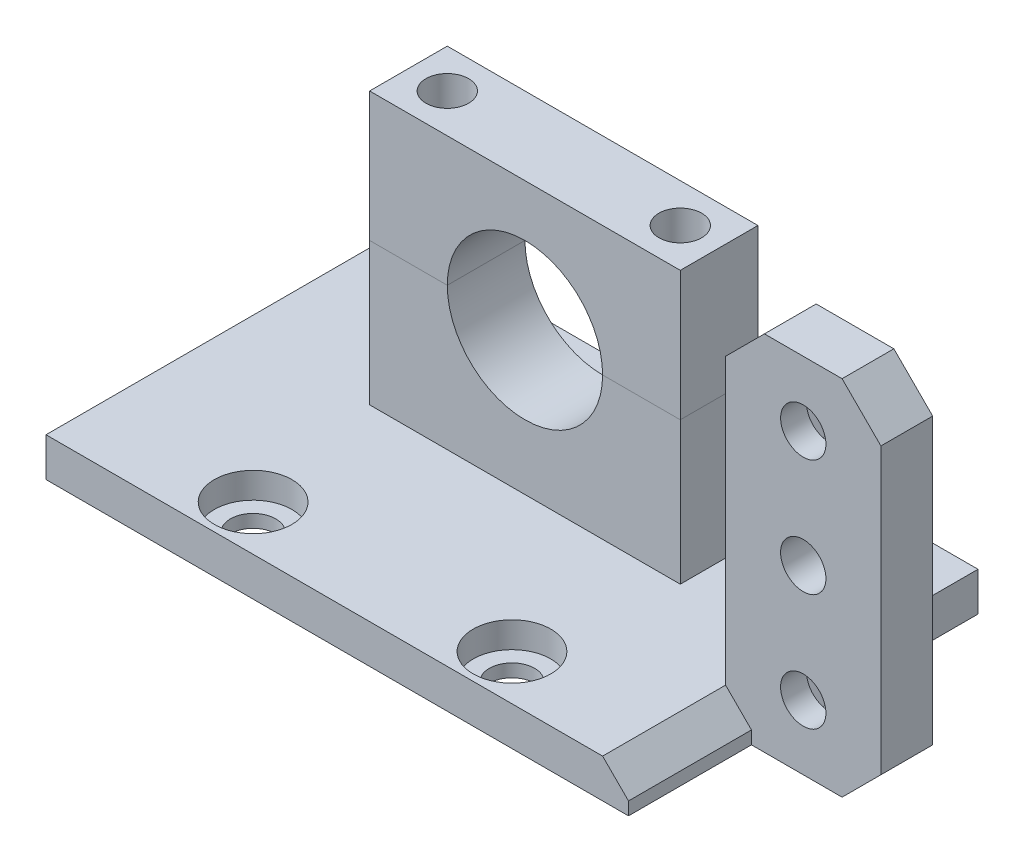
SolidWorks part; units mm, degrees
ref_plane "Front Plane" through (0, 0, 0) normal (0, 0, 1) x (1, 0, 0)
ref_plane "Top Plane" through (0, 0, 0) normal (0, 1, 0) x (1, 0, 0)
ref_plane "Right Plane" through (0, 0, 0) normal (1, 0, 0) x (0, 0, -1)
sketch "Sketch1" plane through (0, 0, 0) normal (0, 1, 0) x (1, 0, 0)
  line L1 (-22.5, -13.5) -> (22.5, -13.5)
  line L2 (-22.5, -13.5) -> (-22.5, 13.5)
  line L3 (-22.5, 13.5) -> (22.5, 13.5)
  line L4 (22.5, -13.5) -> (22.5, 13.5)
  line L5 (-22.5, -13.5) -> (22.5, 13.5) construction
  line L6 (-22.5, 13.5) -> (22.5, -13.5) construction
  point P0 (0, 0)
  dimension "D1" = 27
  dimension "D2" = 45
extrude "Boss-Extrude1" add sketch "Sketch1" along normal blind 3
sketch "Sketch2" plane through (0, 3, 0) normal (0, 1, 0) x (1, 0, 0)
  line L0 (0, 13.5) -> (0, -13.5) construction
  line L1 (22.5, 13.5) -> (-22.5, 13.5) construction
  line L2 (-22.5, -13.5) -> (22.5, -13.5) construction
  line L3 (-22.5, 0) -> (22.5, 0) construction
  line L4 (-22.5, 13.5) -> (-22.5, -13.5) construction
  line L5 (22.5, -13.5) -> (22.5, 13.5) construction
  circle A0 centre (-10, 10) radius 1.75
  circle A1 centre (10, 10) radius 1.75
  circle A2 centre (10, -10) radius 1.75
  circle A3 centre (-10, -10) radius 1.75
  dimension "D1" = 3.5
  dimension "D2" = 10
  dimension "D3" = 10
extrude "Cut-Extrude1" cut sketch "Sketch2" against normal up to next
sketch "Sketch3" plane through (0, 3, 0) normal (0, 1, 0) x (1, 0, 0)
  line L0 (0, 13.5) -> (0, -13.5) construction
  line L1 (22.5, 13.5) -> (-22.5, 13.5) construction
  line L2 (-22.5, -13.5) -> (22.5, -13.5) construction
  line L3 (-22.5, 0) -> (22.5, 0) construction
  line L4 (-22.5, 13.5) -> (-22.5, -13.5) construction
  line L5 (22.5, -13.5) -> (22.5, 13.5) construction
  circle A0 centre (-10, 10) radius 3
  circle A1 centre (10, 10) radius 3
  circle A2 centre (10, -10) radius 3
  circle A3 centre (-10, -10) radius 3
  dimension "D1" = 6
extrude "Cut-Extrude2" cut sketch "Sketch3" against normal blind 2
ref_plane "Plane1" through (0, 0, -4) normal (0, 0, 1) x (1, 0, 0)
sketch "Sketch5" plane through (0, 0, -4) normal (0, 0, 1) x (1, 0, 0)
  line L0 (0, 0) -> (0, 14) construction
  line L1 (22.5, 3) -> (-22.5, 3) construction
  line L2 (12, 3) -> (-12, 3)
  line L3 (-12, 3) -> (-12, 14)
  line L4 (-12, 14) -> (-6, 14)
  line L5 (12, 14) -> (6, 14)
  line L6 (12, 3) -> (12, 14)
  arc A0 (-6, 14) -> (6, 14) centre (0, 14) ccw
  point P13 (0, 3)
  dimension "D3" = 12
  dimension "D1" = 11
  dimension "D2" = 6
extrude "Boss-Extrude2" add sketch "Sketch5" along normal mid plane 6
sketch "Sketch6" plane through (0, 0, -4) normal (0, 0, 1) x (1, 0, 0)
  line L6 (6, 14) -> (12, 14)
  line L7 (-12, 14) -> (-6, 14)
  line L8 (-12, 14) -> (-12, 24)
  line L9 (-12, 24) -> (12, 24)
  line L10 (12, 14) -> (12, 24)
  arc A1 (6, 14) -> (-6, 14) centre (0, 14) ccw
  dimension "D1" = 24
  dimension "D2" = 10
extrude "Boss-Extrude3" add sketch "Sketch6" along normal mid plane 6 separate body
sketch "Sketch7" plane through (0, 24, 0) normal (0, 1, 0) x (1, 0, 0)
  line L0 (-12, 4) -> (12, 4) construction
  line L1 (-12, 1) -> (-12, 7) construction
  line L2 (12, 1) -> (12, 7) construction
  line L3 (0, 7) -> (0, 1) construction
  line L4 (12, 7) -> (-12, 7) construction
  line L5 (-12, 1) -> (12, 1) construction
  circle A0 centre (-9, 4) radius 1.65
  circle A1 centre (9, 4) radius 1.65
  dimension "D1" = 3.3
  dimension "D2" = 3
extrude "Cut-Extrude3" cut sketch "Sketch7" against normal blind 15
sketch "Sketch8" plane through (0, 3, 0) normal (0, 1, 0) x (1, 0, 0)
  line L0 (-22.5, -13.5) -> (22.5, -13.5) construction
  line L1 (20.5, -4) -> (32.5, -4)
  line L2 (20.5, -4) -> (20.5, 0)
  line L3 (20.5, 0) -> (32.5, 0)
  line L4 (32.5, -4) -> (32.5, 0)
  line L5 (22.5, -13.5) -> (22.5, 13.5) construction
  dimension "D1" = 4
  dimension "D2" = 9.5
  dimension "D3" = 2
  dimension "D4" = 12
extrude "Boss-Extrude4" add sketch "Sketch8" along normal blind 25 and the other way up to surface (3 mm away) other way up to face at (-10, 0, 8.25)
sketch "Sketch9" plane through (0, 0, 0) normal (0, 0, -1) x (-1, 0, 0)
  line L0 (-20.5, 5) -> (-32.5, 5) construction
  line L1 (-20.5, 3) -> (-20.5, 28) construction
  line L2 (-32.5, 0) -> (-32.5, 28) construction
  line L3 (-22.5, 3) -> (22.5, 3) construction
  circle A0 centre (-26.5, 5) radius 1.75
  circle A1 centre (-26.5, 14) radius 1.75
  circle A2 centre (-26.5, 23) radius 1.75
  dimension "D2" = 3.5
  dimension "D4" = 9
  dimension "D1" = 2
  dimension "D3" = 3
extrude "Cut-Extrude4" cut sketch "Sketch9" against normal up to next (4 mm away)
sketch "Sketch10" plane through (0, 0, 0) normal (0, 0, -1) x (-1, 0, 0)
  line L0 (-26.5, 14) -> (-32.5, 14) construction
  line L1 (-29.8486, 5) -> (-28.1743, 2.1)
  line L2 (-28.1743, 2.1) -> (-24.8257, 2.1)
  line L3 (-24.8257, 2.1) -> (-23.1514, 5)
  line L4 (-23.1514, 5) -> (-24.8257, 7.9)
  line L5 (-24.8257, 7.9) -> (-28.1743, 7.9)
  line L6 (-28.1743, 7.9) -> (-29.8486, 5)
  line L7 (-32.5, 0) -> (-32.5, 28) construction
  line L8 (-28.1743, 20.1) -> (-29.8486, 23)
  line L9 (-24.8257, 20.1) -> (-28.1743, 20.1)
  line L10 (-23.1514, 23) -> (-24.8257, 20.1)
  line L11 (-24.8257, 25.9) -> (-23.1514, 23)
  line L12 (-28.1743, 25.9) -> (-24.8257, 25.9)
  line L13 (-29.8486, 23) -> (-28.1743, 25.9)
  circle A0 centre (-26.5, 5) radius 2.9 construction
  dimension "D1" = 5.8
  dimension "D2" = 2.9
extrude "Cut-Extrude5" cut sketch "Sketch10" against normal blind 2
chamfer "Chamfer1" distance 2 angle 45 1 edges at (22.5, 3, 8.75)
chamfer "Chamfer2" distance 3 angle 45 3 edges at (32.5, 28, 2) (20.5, 28, 2) (32.5, 0, 2)
